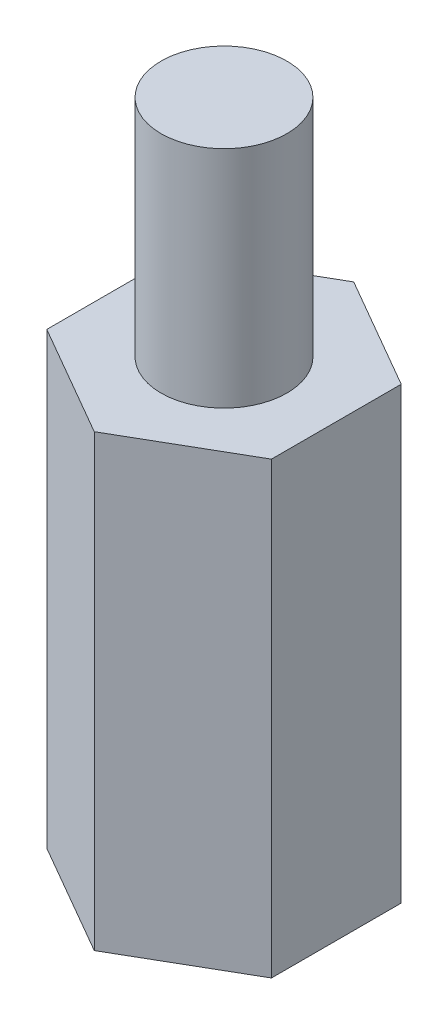
SolidWorks part; units mm, degrees
ref_plane "Front Plane" through (0, 0, 0) normal (0, 0, 1) x (1, 0, 0)
ref_plane "Top Plane" through (0, 0, 0) normal (0, 1, 0) x (1, 0, 0)
ref_plane "Right Plane" through (0, 0, 0) normal (1, 0, 0) x (0, 0, -1)
sketch "Sketch1" plane through (0, 0, 0) normal (0, 1, 0) x (1, 0, 0)
  line L1 (0, 3.6662) -> (-3.175, 1.8331)
  line L2 (-3.175, 1.8331) -> (-3.175, -1.8331)
  line L3 (-3.175, -1.8331) -> (0, -3.6662)
  line L4 (0, -3.6662) -> (3.175, -1.8331)
  line L5 (3.175, -1.8331) -> (3.175, 1.8331)
  line L6 (3.175, 1.8331) -> (0, 3.6662)
  circle A0 centre (0, 0) radius 3.175 construction
  dimension "D1" = 6.35
extrude "Boss-Extrude1" add sketch "Sketch1" along normal blind 12.7
sketch "Sketch2" plane through (0, 12.7, 0) normal (0, 1, 0) x (1, 0, 0)
  circle A0 centre (0, 0) radius 1.778
extrude "Boss-Extrude2" add sketch "Sketch2" along normal blind 6.35
